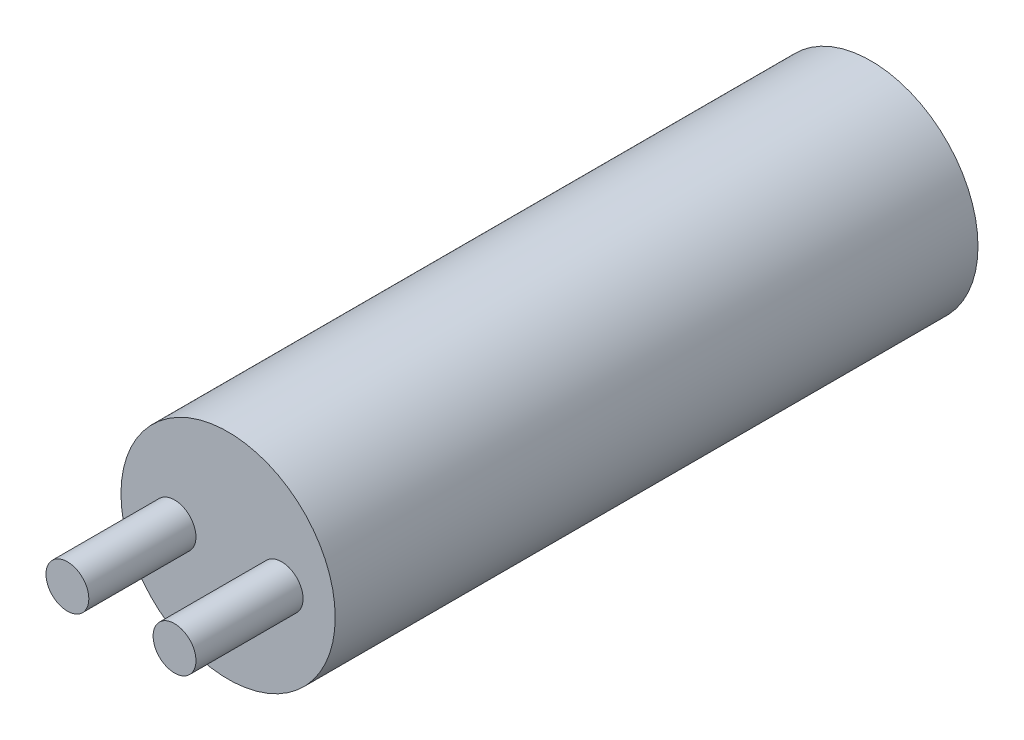
SolidWorks part; units mm, degrees
ref_plane "Front Plane" through (0, 0, 0) normal (0, 0, 1) x (1, 0, 0)
ref_plane "Top Plane" through (0, 0, 0) normal (0, 1, 0) x (1, 0, 0)
ref_plane "Right Plane" through (0, 0, 0) normal (1, 0, 0) x (0, 0, -1)
sketch "Sketch2" plane through (0, 0, 0) normal (0, 0, 1) x (1, 0, 0)
  circle A0 centre (0, 0) radius 12.7
  dimension "D1" = 25.4
extrude "Boss-Extrude1" add sketch "Sketch2" along normal blind 101.6
sketch "Sketch3" plane through (0, 0, 101.6) normal (0, 0, 1) x (1, 0, 0)
  line L0 (0, 0) -> (12.7, 0)
  line L1 (12.7, 0) -> (-12.7, 0)
  line L2 (-12.7, 0) -> (0, 0)
  circle A0 centre (0, 0) radius 12.7 construction
  circle A1 centre (-6.35, 0) radius 2.54
  circle A2 centre (6.35, 0) radius 2.54
  dimension "D1" = 5.08
  dimension "D2" = 5.08
extrude "Boss-Extrude2" add sketch "Sketch3" along normal blind 12.7 contours L2 A1 | L2 A1 | L1 A2 | L1 A2
sketch "Sketch4" plane through (0, 0, 0) normal (0, 0, -1) x (-1, 0, 0)
  circle A0 centre (0, 0) radius 14.1963
extrude "Cut-Extrude1" cut sketch "Sketch4" against normal blind 25.4
